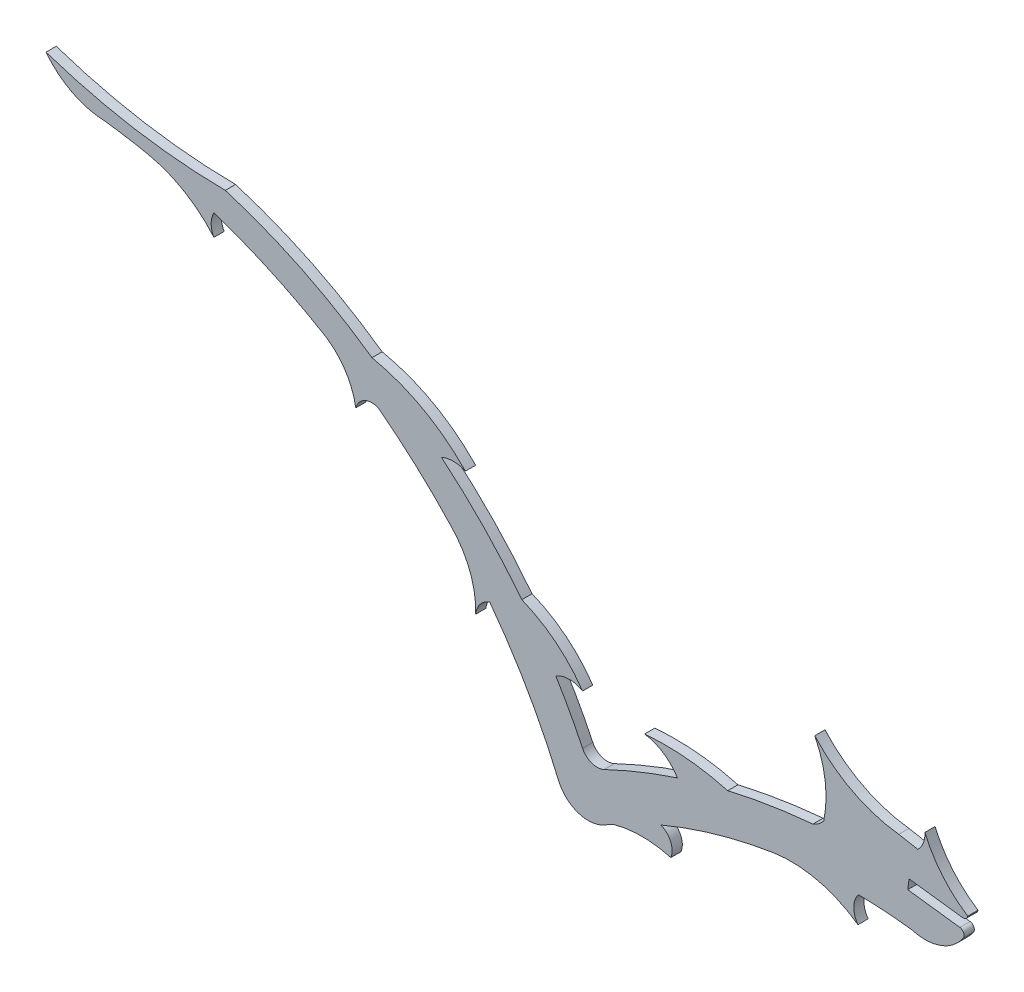
SolidWorks part; units mm, degrees
ref_plane "Front Plane" through (0, 0, 0) normal (0, 0, 1) x (1, 0, 0)
ref_plane "Top Plane" through (0, 0, 0) normal (0, 1, 0) x (1, 0, 0)
ref_plane "Right Plane" through (0, 0, 0) normal (1, 0, 0) x (0, 0, -1)
sketch "Sketch1" plane through (0, 0, 0) normal (0, 0, 1) x (1, 0, 0)
  line L0 (66.8177, -14.8692) -> (59.0562, -13.8769)
  line L1 (59.0562, -13.8769) -> (59.247, -12.383)
  line L2 (59.247, -12.383) -> (67.1948, -13.3984)
  line L3 (60.5544, -7.9282) -> (57.7081, -7.4038)
  arc A0 (44.9171, -12.4813) -> (46.5321, -11.2582) centre (43.6867, -9.1788) ccw
  arc A1 (44.9171, -12.4813) -> (32.2193, -14.5201) centre (52.9027, -102.7776) ccw
  arc A2 (10.59, -19.8589) -> (13.8043, -20.9944) centre (12.7647, -18.8198) ccw
  arc A3 (10.59, -19.8589) -> (6.6046, -12.5264) centre (-61.6896, -54.3946) ccw
  arc A4 (-20.7965, 14.8535) -> (-42.6474, 25.5211) centre (-64.6226, -47.2046) ccw
  arc A5 (67.9958, -12.8216) -> (61.6076, -5.2099) centre (77.1236, 1.3256) cw
  arc A6 (7.013, -25.8177) -> (-3.2502, -7.9003) centre (-71.2484, -58.748) ccw
  arc A7 (7.013, -25.8177) -> (13.883, -28.1132) centre (11.4562, -23.9482) ccw
  arc A8 (59.6197, -18.748) -> (51.6935, -18.1989) centre (50.621, -91.1655) ccw
  arc A9 (59.6197, -18.748) -> (67.3267, -15.9889) centre (61.6076, -12.1571) ccw
  arc A10 (67.3267, -15.9889) -> (66.8177, -14.8692) centre (66.726, -15.5864) ccw
  arc A11 (67.1948, -13.3984) -> (67.9958, -12.8216) centre (67.2865, -12.6811) ccw
  arc A13 (32.2193, -14.5201) -> (19.8323, -13.3984) centre (22.913, -48.3319) ccw
  arc A14 (-54.152, 24.4203) -> (-44.3461, 18.6098) centre (-57.748, 7.1719) cw
  arc A15 (-44.3461, 18.6098) -> (-44.3461, 21.7847) centre (-41.497, 20.1973) cw
  arc A16 (-27.4775, 14.0075) -> (-23.207, 7.1719) centre (-33.463, 5.5163) cw
  arc A17 (-23.207, 7.1719) -> (-19.8906, 8.8658) centre (-20.7965, 6.5459) cw
  arc A18 (-9.0664, -0.9324) -> (-5.3364, -10.5277) centre (-18.3414, -10.0605) cw
  arc A19 (-5.3364, -10.5277) -> (-3.2502, -7.9003) centre (-2.2302, -10.8522) cw
  arc A20 (-54.152, 24.4203) -> (-60.4369, 25.4682) centre (-71.2484, -58.748) ccw
  arc A21 (-27.4775, 14.0075) -> (-44.3461, 21.7847) centre (-71.2484, -58.748) ccw
  arc A22 (-9.0664, -0.9324) -> (-19.8906, 8.8658) centre (-71.2484, -58.748) ccw
  arc A23 (15.134, -27.4008) -> (23.7428, -27.4008) centre (19.4384, -42.6453) cw
  arc A24 (23.7428, -27.4008) -> (22.276, -23.9209) centre (21.2385, -26.4073) ccw
  arc A25 (39.0646, -19.1119) -> (51.6361, -22.1097) centre (41.6372, -36.182) cw
  arc A26 (51.6361, -22.1097) -> (51.6935, -18.1989) centre (54.2438, -20.1922) cw
  arc A27 (39.0646, -19.1119) -> (22.276, -23.9209) centre (50.621, -91.1655) ccw
  arc A28 (15.134, -27.4008) -> (13.883, -28.1132) centre (50.621, -91.1655) ccw
  arc A29 (57.7081, -7.4038) -> (45.1933, -0.9324) centre (59.977, 12.3204) cw
  arc A30 (45.1933, -0.9324) -> (46.5321, -11.2582) centre (31.26, -7.9887) cw
  arc A31 (19.8323, -13.3984) -> (24.7254, -16.6195) centre (18.8291, -20.2494) cw
  arc A32 (24.7254, -16.6195) -> (13.8043, -20.9944) centre (52.9027, -102.7776) ccw
  arc A33 (1.5395, -5.2099) -> (10.59, -12.4813) centre (-5.9066, -23.746) cw
  arc A34 (10.59, -12.4813) -> (6.6046, -12.5264) centre (8.6347, -15.8136) ccw
  arc A35 (1.5395, -5.2099) -> (-10.4391, 7.1719) centre (-61.6896, -54.3946) ccw
  arc A36 (-20.7965, 14.8535) -> (-6.8673, 7.1719) centre (-26.1774, -11.3739) cw
  arc A37 (-6.8673, 7.1719) -> (-10.4391, 7.1719) centre (-8.6532, 3.1743) ccw
  arc A38 (-42.6474, 25.5211) -> (-69.3715, 30.0005) centre (-41.96, 111.5792) cw
  arc A39 (-69.3715, 30.0005) -> (-60.4369, 25.4682) centre (-60.1361, 37.1336) ccw
  arc A40 (61.6076, -5.2099) -> (60.5544, -7.9282) centre (58.0902, -5.4103) cw
extrude "Boss-Extrude1" add sketch "Sketch1" along normal blind 1.524
